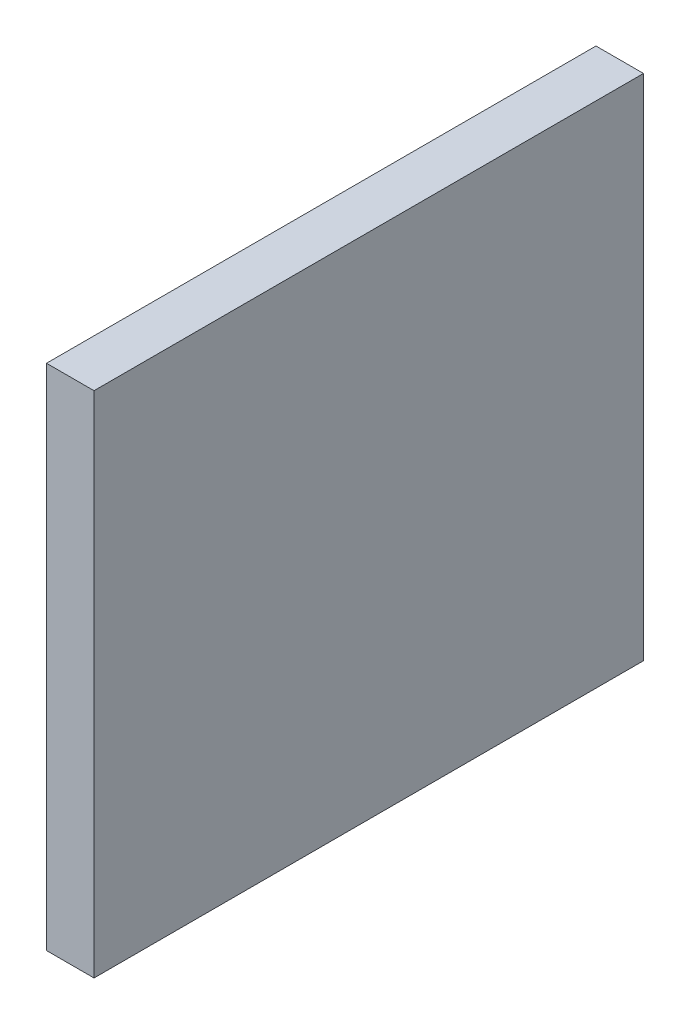
SolidWorks part; units mm, degrees
ref_plane "Front Plane" through (0, 0, 0) normal (0, 0, 1) x (1, 0, 0)
ref_plane "Top Plane" through (0, 0, 0) normal (0, 1, 0) x (1, 0, 0)
ref_plane "Right Plane" through (0, 0, 0) normal (1, 0, 0) x (0, 0, -1)
sketch "Sketch2" plane through (0, 0, -331.8) normal (0, 0, 1) x (1, 0, 0)
  line L0 (-113.6, 0) -> (-118.6, 0)
  line L1 (-113.6, 0) -> (-113.6, -53.5024)
  line L2 (-118.6, 0) -> (-118.6, -53.5024)
  line L3 (-113.6, -53.5024) -> (-118.6, -53.5024)
  line L4 (-249.6, 0) -> (0, 0) construction
  line L7 (-116.1, 0) -> (-116.1, -350.4) construction
  point P8 (-116.1, -53.5024)
  dimension "D1" = 5
extrude "Boss-Extrude1" add sketch "Sketch2" along normal up to surface (57.8 mm away)
